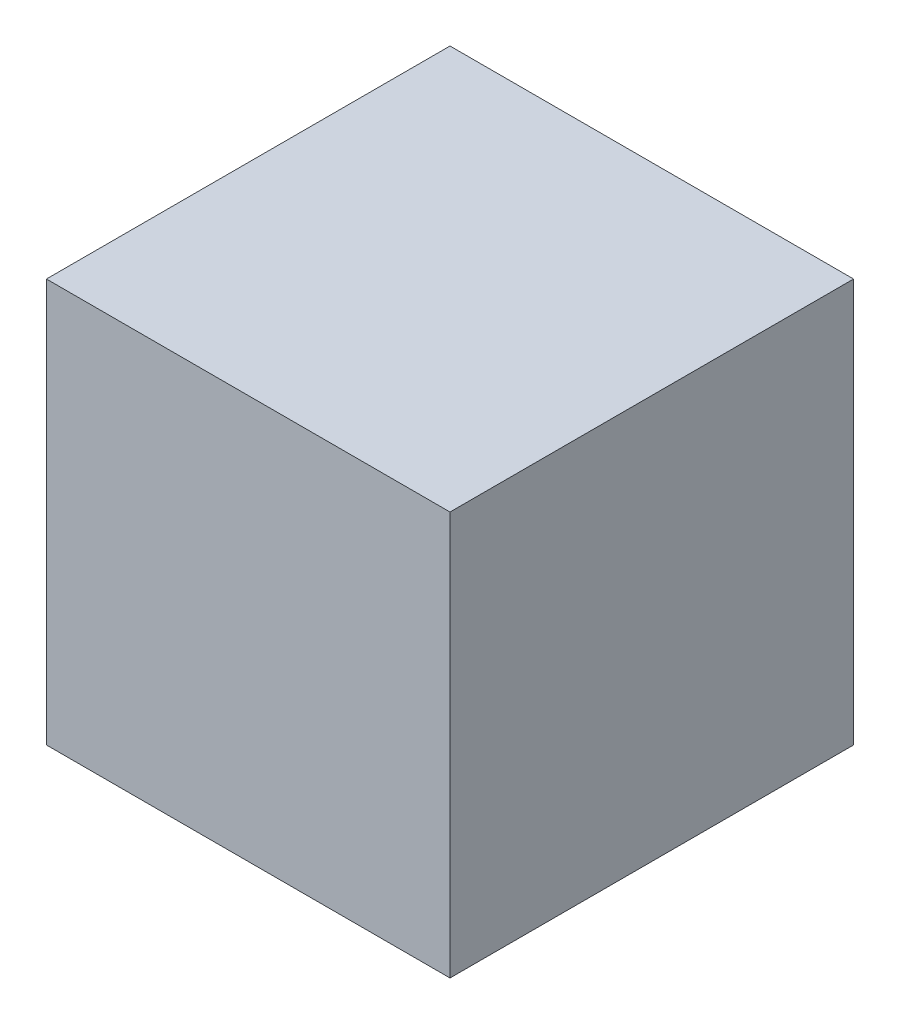
SolidWorks part; units mm, degrees
ref_plane "Front Plane" through (0, 0, 0) normal (0, 0, 1) x (1, 0, 0)
ref_plane "Top Plane" through (0, 0, 0) normal (0, 1, 0) x (1, 0, 0)
ref_plane "Right Plane" through (0, 0, 0) normal (1, 0, 0) x (0, 0, -1)
sketch "Sketch1" plane through (0, 0, 0) normal (0, 0, 1) x (1, 0, 0)
  line L1 (-254.0005, -254.0005) -> (254.0005, -254.0005)
  line L2 (-254.0005, -254.0005) -> (-254.0005, 254.0005)
  line L3 (-254.0005, 254.0005) -> (254.0005, 254.0005)
  line L4 (254.0005, -254.0005) -> (254.0005, 254.0005)
  line L5 (-254.0005, -254.0005) -> (254.0005, 254.0005) construction
  line L6 (-254.0005, 254.0005) -> (254.0005, -254.0005) construction
  point P0 (0, 0)
  dimension "D1" = 508.001
  dimension "D2" = 508.001
extrude "Boss-Extrude1" add sketch "Sketch1" along normal blind 508.001 contours L3 L4 L1 L2
